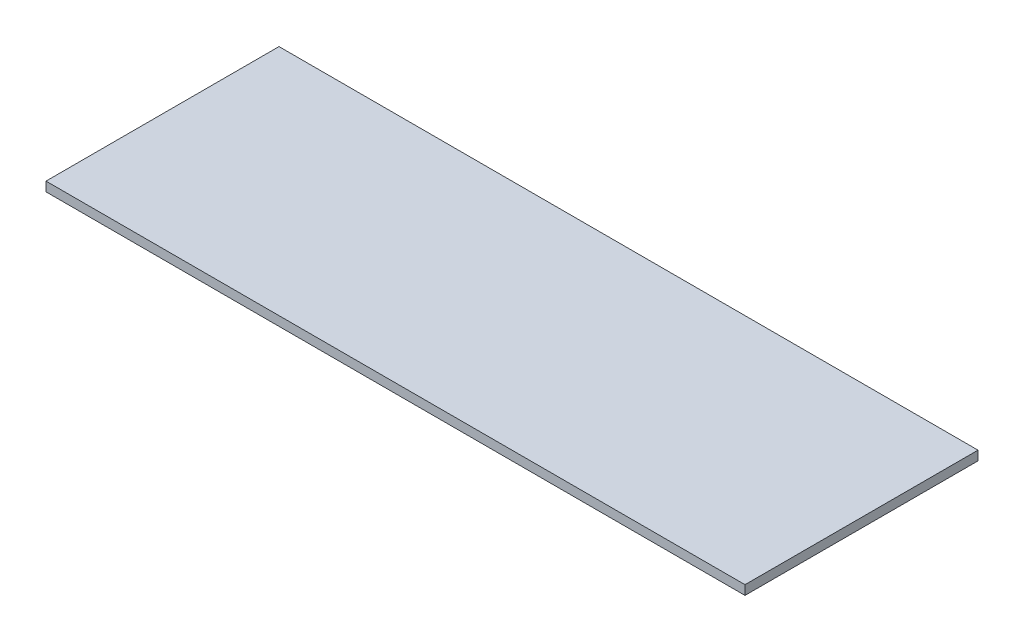
SolidWorks part; units mm, degrees
ref_plane "Front Plane" through (0, 0, 0) normal (0, 0, 1) x (1, 0, 0)
ref_plane "Top Plane" through (0, 0, 0) normal (0, 1, 0) x (1, 0, 0)
ref_plane "Right Plane" through (0, 0, 0) normal (1, 0, 0) x (0, 0, -1)
sketch "Sketch1" plane through (0, 0, 0) normal (0, 1, 0) x (1, 0, 0)
  line L1 (0, 0) -> (75, 0)
  line L2 (0, 0) -> (0, 25)
  line L3 (0, 25) -> (75, 25)
  line L4 (75, 0) -> (75, 25)
  dimension "D1" = 75
  dimension "D2" = 25
extrude "Boss-Extrude1" add sketch "Sketch1" along normal blind 1
